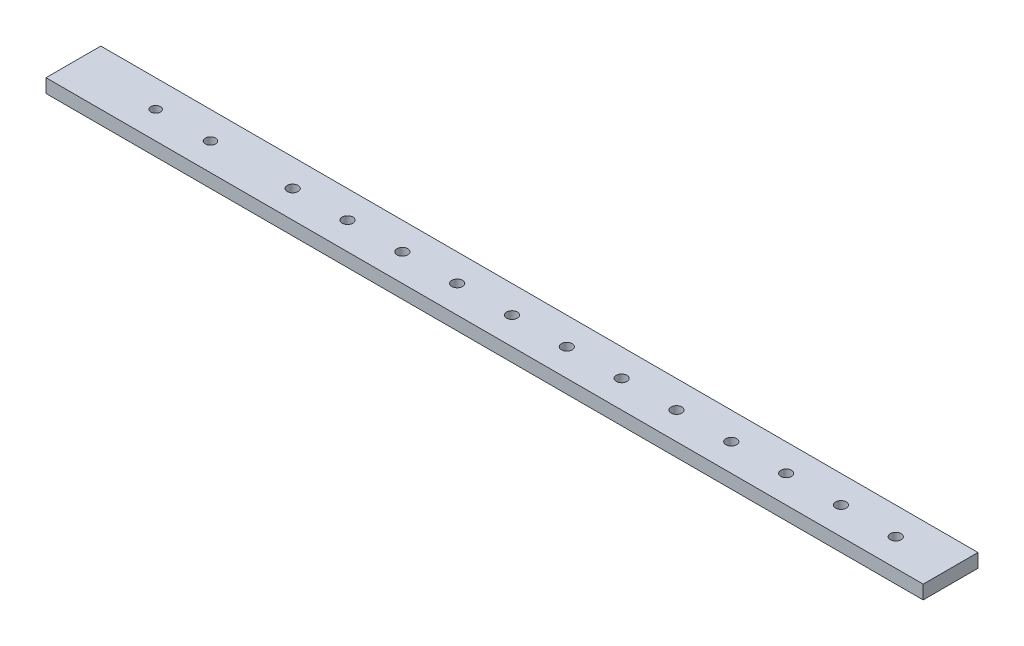
SolidWorks part; units mm, degrees
material "Lexan"
ref_plane "Front Plane" through (0, 0, 0) normal (0, 0, 1) x (1, 0, 0)
ref_plane "Top Plane" through (0, 0, 0) normal (0, 1, 0) x (1, 0, 0)
ref_plane "Right Plane" through (0, 0, 0) normal (1, 0, 0) x (0, 0, -1)
sketch "Sketch1" plane through (0, 0, 0) normal (0, 1, 0) x (1, 0, 0)
  line L1 (0, 0) -> (406.4, 0)
  line L2 (0, 0) -> (0, 25.4)
  line L3 (0, 25.4) -> (406.4, 25.4)
  line L4 (406.4, 0) -> (406.4, 25.4)
  dimension "D1" = 25.4
  dimension "D2" = 406.4
extrude "Boss-Extrude1" add sketch "Sketch1" along normal blind 6.35
sketch "Sketch2" plane through (0, 6.35, 0) normal (0, 1, 0) x (1, 0, 0)
  line L0 (406.4, 12.7) -> (0, 12.7) construction
  line L1 (406.4, 0) -> (406.4, 25.4) construction
  line L2 (0, 25.4) -> (0, 0) construction
  circle A0 centre (381, 12.7) radius 2.4892
  circle A1 centre (355.6, 12.7) radius 2.4892
  circle A2 centre (330.2, 12.7) radius 2.4892
  circle A3 centre (304.8, 12.7) radius 2.4892
  circle A4 centre (279.4, 12.7) radius 2.4892
  circle A5 centre (254, 12.7) radius 2.4892
  circle A6 centre (228.6, 12.7) radius 2.4892
  circle A7 centre (203.2, 12.7) radius 2.4892
  circle A8 centre (177.8, 12.7) radius 2.4892
  circle A9 centre (152.4, 12.7) radius 2.4892
  circle A10 centre (127, 12.7) radius 2.4892
  circle A11 centre (101.6, 12.7) radius 2.4892
  dimension "D1" = 25.4
  dimension "D2" = 4.9784
  dimension "D3" = 12
extrude "Cut-Extrude1" cut sketch "Sketch2" against normal through all both
sketch "Sketch3" plane through (0, 0, 0) normal (0, -1, 0) x (1, 0, 0)
  circle A2 centre (63.5, -12.7) radius 2.3781
  circle A3 centre (38.1, -12.7) radius 2.2074
extrude "Cut-Extrude2" cut sketch "Sketch3" against normal through all
